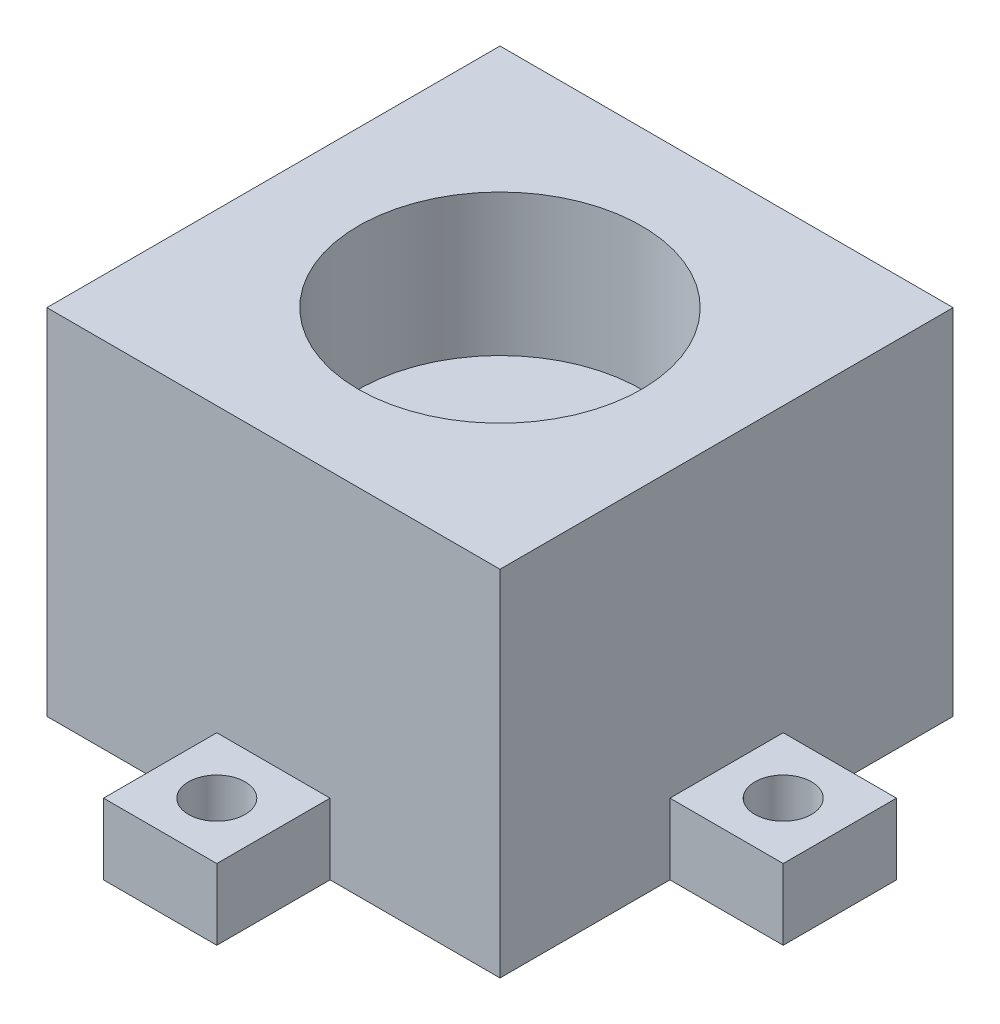
SolidWorks part; units mm, degrees
ref_plane "Front Plane" through (0, 0, 0) normal (0, 0, 1) x (1, 0, 0)
ref_plane "Top Plane" through (0, 0, 0) normal (0, 1, 0) x (1, 0, 0)
ref_plane "Right Plane" through (0, 0, 0) normal (1, 0, 0) x (0, 0, -1)
sketch "Sketch1" plane through (0, 0, 0) normal (0, 1, 0) x (1, 0, 0)
  line L0 (20.32, 40.64) -> (20.32, 0) construction
  line L1 (0, 0) -> (40.64, 0)
  line L2 (0, 0) -> (0, 40.64)
  line L3 (0, 40.64) -> (40.64, 40.64)
  line L4 (40.64, 0) -> (40.64, 40.64)
  line L5 (0, 20.32) -> (40.64, 20.32) construction
  line L6 (15.24, 50.8) -> (25.4, 50.8)
  line L7 (15.24, 50.8) -> (15.24, 40.64)
  line L8 (15.24, 40.64) -> (25.4, 40.64)
  line L9 (25.4, 50.8) -> (25.4, 40.64)
  line L10 (25.4, -10.16) -> (25.4, 0)
  line L11 (15.24, 0) -> (25.4, 0)
  line L12 (15.24, -10.16) -> (15.24, 0)
  line L13 (15.24, -10.16) -> (25.4, -10.16)
  line L14 (40.64, 25.4) -> (50.8, 25.4)
  line L15 (40.64, 25.4) -> (40.64, 15.24)
  line L16 (40.64, 15.24) -> (50.8, 15.24)
  line L17 (50.8, 25.4) -> (50.8, 15.24)
  line L19 (-10.16, 25.4) -> (0, 25.4)
  line L20 (-10.16, 25.4) -> (-10.16, 15.24)
  line L21 (-10.16, 15.24) -> (0, 15.24)
  line L22 (0, 25.4) -> (0, 15.24)
  dimension "D1" = 40.64
  dimension "D2" = 40.64
  dimension "D3" = 10.16
  dimension "D4" = 10.16
  dimension "D5" = 5.08
  dimension "D6" = 10.16
  dimension "D7" = 5.08
  dimension "D8" = 10.16
  dimension "D9" = 10.16
  dimension "D10" = 10.16
  dimension "D11" = 5.08
extrude "Boss-Extrude1" add sketch "Sketch1" along normal blind 6.35 contours L20 L21 L2 L19 | L9 L6 L7 L3 | L1 L4 L3 L2 | L17 L14 L4 L16 | L12 L13 L10 L1
sketch "Sketch2" plane through (0, 6.35, 0) normal (0, 1, 0) x (1, 0, 0)
  line L0 (-5.08, 25.4) -> (-5.08, 15.24) construction
  line L1 (-10.16, 25.4) -> (0, 25.4) construction
  line L2 (-10.16, 15.24) -> (0, 15.24) construction
  line L3 (-10.16, 20.32) -> (50.8, 20.32) construction
  line L4 (-10.16, 25.4) -> (-10.16, 15.24) construction
  line L5 (50.8, 25.4) -> (50.8, 15.24) construction
  line L6 (20.32, 50.8) -> (20.32, -10.16) construction
  line L7 (15.24, 50.8) -> (25.4, 50.8) construction
  line L8 (15.24, -10.16) -> (25.4, -10.16) construction
  line L9 (25.4, -5.08) -> (15.24, -5.08) construction
  line L10 (25.4, -10.16) -> (25.4, 0) construction
  line L11 (15.24, -10.16) -> (15.24, 0) construction
  line L12 (45.72, 15.24) -> (45.72, 25.4) construction
  line L13 (40.64, 15.24) -> (50.8, 15.24) construction
  line L14 (40.64, 25.4) -> (50.8, 25.4) construction
  line L15 (15.24, 45.72) -> (25.4, 45.72) construction
  line L16 (15.24, 50.8) -> (15.24, 40.64) construction
  line L17 (25.4, 50.8) -> (25.4, 40.64) construction
  circle A0 centre (-5.08, 20.32) radius 2.54
  circle A1 centre (20.32, 45.72) radius 2.54
  circle A2 centre (45.72, 20.32) radius 2.54
  circle A3 centre (20.32, -5.08) radius 2.54
  point P44 (0, 0)
  dimension "D1" = 5.08
  dimension "D2" = 5.08
  dimension "D3" = 5.08
  dimension "D4" = 5.08
extrude "Cut-Extrude1" cut sketch "Sketch2" against normal blind 8.89
sketch "Sketch3" plane through (0, 6.35, 0) normal (0, 1, 0) x (1, 0, 0)
  line L1 (0, 40.64) -> (40.64, 40.64)
  line L2 (0, 40.64) -> (0, 0)
  line L3 (0, 0) -> (40.64, 0)
  line L4 (40.64, 40.64) -> (40.64, 0)
extrude "body_extrude" add sketch "Sketch3" along normal blind 25.4
sketch "Sketch4" plane through (0, 31.75, 0) normal (0, 1, 0) x (1, 0, 0)
  line L0 (20.32, 40.64) -> (20.32, 0) construction
  line L1 (40.64, 40.64) -> (0, 40.64) construction
  line L2 (15.24, 0) -> (25.4, 0) construction
  line L3 (0, 20.32) -> (40.64, 20.32) construction
  line L4 (0, 25.4) -> (0, 15.24) construction
  line L5 (40.64, 15.24) -> (40.64, 25.4) construction
  circle A0 centre (20.32, 20.32) radius 12.7
  dimension "D1" = 25.4
extrude "motor_hole" cut sketch "Sketch4" against normal blind 12.7
